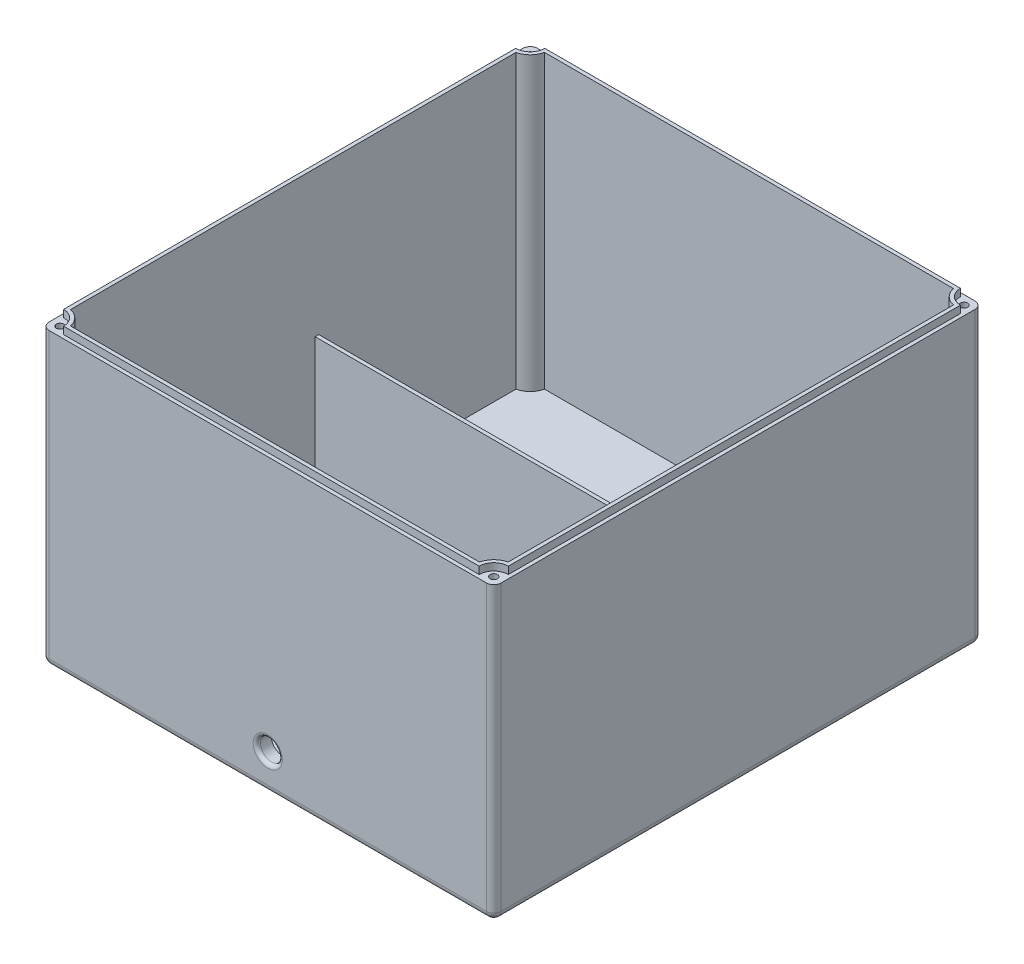
SolidWorks part; units mm, degrees
ref_plane "Front Plane" through (0, 0, 0) normal (0, 0, 1) x (1, 0, 0)
ref_plane "Top Plane" through (0, 0, 0) normal (0, 1, 0) x (1, 0, 0)
ref_plane "Right Plane" through (0, 0, 0) normal (1, 0, 0) x (0, 0, -1)
sketch "Sketch1" plane through (0, 0, 0) normal (0, 1, 0) x (1, 0, 0)
  line L1 (62, 67) -> (-62, 67)
  line L2 (62, 67) -> (62, -67)
  line L3 (62, -67) -> (-62, -67)
  line L4 (-62, 67) -> (-62, -67)
  line L5 (62, 67) -> (-62, -67) construction
  line L6 (62, -67) -> (-62, 67) construction
  point P0 (0, 0)
  dimension "D1" = 124
  dimension "D2" = 134
extrude "Boss-Extrude1" add sketch "Sketch1" along normal blind 80
sketch "Sketch2" plane through (0, 80, 0) normal (0, 1, 0) x (1, 0, 0)
  line L0 (-62, 67) -> (-62, -67) construction
  line L1 (57, 66) -> (-57, 66)
  line L2 (61, 62) -> (61, -62)
  line L3 (57, -66) -> (-57, -66)
  line L4 (-61, 62) -> (-61, -62)
  line L5 (61, 66) -> (-61, -66) construction
  line L6 (61, -66) -> (-61, 66) construction
  line L7 (62, 67) -> (-62, 67) construction
  line L8 (62, -67) -> (62, 67) construction
  line L10 (-62, -67) -> (62, -67) construction
  arc A0 (-61, 62) -> (-57, 66) centre (-61, 66) ccw
  arc A1 (57, 66) -> (61, 62) centre (61, 66) ccw
  arc A2 (61, -62) -> (57, -66) centre (61, -66) ccw
  arc A3 (-57, -66) -> (-61, -62) centre (-61, -66) ccw
  point P0 (0, 0)
  dimension "D3" = 8
  dimension "D4" = 8
  dimension "D5" = 8
  dimension "D6" = 8
  dimension "D7" = 1
  dimension "D8" = 5
  dimension "D1" = 1
  dimension "D2" = 1
  dimension "D9" = 5
  dimension "D10" = 5
  dimension "D11" = 1
  dimension "D12" = 1
  dimension "D13" = 1
  dimension "D14" = 1
extrude "Boss-Extrude2" add sketch "Sketch2" along normal blind 2
sketch "Sketch3" plane through (0, 82, 0) normal (0, 1, 0) x (1, 0, 0)
  line L12 (56.101, 65) -> (-56.101, 65)
  line L13 (-60, 61.101) -> (-60, -61.101)
  line L14 (-56.101, -65) -> (56.101, -65)
  line L15 (60, -61.101) -> (60, 61.101)
  line L16 (56.101, 65) -> (-56.101, 65)
  line L17 (-60, 61.101) -> (-60, -61.101)
  line L18 (-56.101, -65) -> (56.101, -65)
  line L19 (60, -61.101) -> (60, 61.101)
  arc A12 (56.101, 65) -> (60, 61.101) centre (61, 66) ccw
  arc A13 (-60, 61.101) -> (-56.101, 65) centre (-61, 66) ccw
  arc A14 (-56.101, -65) -> (-60, -61.101) centre (-61, -66) ccw
  arc A15 (60, -61.101) -> (56.101, -65) centre (61, -66) ccw
  arc A16 (56.101, 65) -> (60, 61.101) centre (61, 66) ccw
  arc A17 (-60, 61.101) -> (-56.101, 65) centre (-61, 66) ccw
  arc A18 (-56.101, -65) -> (-60, -61.101) centre (-61, -66) ccw
  arc A19 (60, -61.101) -> (56.101, -65) centre (61, -66) ccw
  dimension "D1" = 1
extrude "Cut-Extrude3" cut sketch "Sketch3" against normal blind 80
fillet "Fillet1" radius 2 8 edges at (62, 0, 0) (0, 0, 67) (-62, 0, 0) (0, 0, -67) (-62, 40, -67) (62, 40, -67) (62, 40, 67) (-62, 40, 67)
sketch "Sketch5" plane through (0, 0, 67) normal (0, 0, 1) x (1, 0, 0)
  line L0 (-62, 2) -> (-62, 80) construction
  line L1 (60, 0) -> (-60, 0) construction
  circle A0 centre (0, 10) radius 4
  dimension "D1" = 8
  dimension "D2" = 62
  dimension "D3" = 10
extrude "Boss-Extrude4" add sketch "Sketch5" against normal blind 4
sketch "Sketch9" plane through (0, 0, -67) normal (0, 0, -1) x (-1, 0, 0)
  line L0 (-62, 2) -> (-62, 80) construction
  line L2 (60, 0) -> (-60, 0) construction
  circle A0 centre (0, 10) radius 4
  dimension "D3" = 8
  dimension "D1" = 62
  dimension "D2" = 10
extrude "Boss-Extrude5" add sketch "Sketch9" against normal blind 4
sketch "Sketch10" plane through (0, 0, -67) normal (0, 0, -1) x (-1, 0, 0)
  line L0 (-62, 2) -> (-62, 80) construction
  line L2 (60, 0) -> (-60, 0) construction
  circle A0 centre (0, 10) radius 3
  dimension "D3" = 6
  dimension "D1" = 62
  dimension "D2" = 10
extrude "Cut-Extrude5" cut sketch "Sketch10" against normal through all both and the other way through all
fillet "Fillet3" radius 1 2 edges at (-3, 10, 67) (3, 10, -67)
hole_wizard "Ø2.0mm Dowel Hole1" positions "3DSketch2" profile "Sketch11" hole size "Ø2.0" standard "ANSI Metric"
sketch3d "3DSketch2"
  line L0 (60, 80, -67) -> (-60, 80, -67) construction
  line L1 (-62, 80, -65) -> (-62, 80, 65) construction
  line L2 (62, 80, 65) -> (62, 80, -65) construction
  line L3 (-60, 80, 67) -> (60, 80, 67) construction
  point P0 (59.5, 80, -64.5)
  point P2 (59.5, 80, 64.5)
  point P4 (-59.5, 80, 64.5)
  point P6 (-59.5, 80, -64.5)
  dimension "D1" = 2.5
  dimension "D2" = 2.5
  dimension "D3" = 2.5
  dimension "D4" = 2.5
  dimension "D5" = 2.5
  dimension "D6" = 2.5
  dimension "D7" = 2.5
  dimension "D8" = 2.5
sketch "Sketch11" plane through (59.5, 80, -64.5) normal (1, 0, 0) x (0, 0, 1)
  line L0 (0, 0) -> (0, 20.6009)
  line L1 (0, 20.6009) -> (1, 20)
  line L2 (1, 20) -> (1, 0)
  line L5 (1, 0) -> (0, 0)
  line L10 (0, 20.6009) -> (-1, 20) construction
  line L11 (0, -6.35) -> (0, 107.95) construction
  dimension "Hole Dia." = 2
  dimension "Hole Depth" = 20
  dimension "Drill Angle" = 118
sketch "Sketch14" plane through (0, 2, 0) normal (0, 1, 0) x (1, 0, 0)
  line L0 (60, 6) -> (-60, 6)
  line L1 (60, -61.101) -> (60, 61.101) construction
  line L2 (-60, 61.101) -> (-60, -61.101) construction
  line L3 (-60, 6) -> (-60, 7)
  line L4 (-60, 7) -> (60, 7)
  line L5 (60, 7) -> (60, 6)
  line L6 (56.101, 65) -> (-56.101, 65) construction
  dimension "D1" = 58
  dimension "D2" = 1
extrude "Boss-Extrude6" add sketch "Sketch14" along normal blind 40
